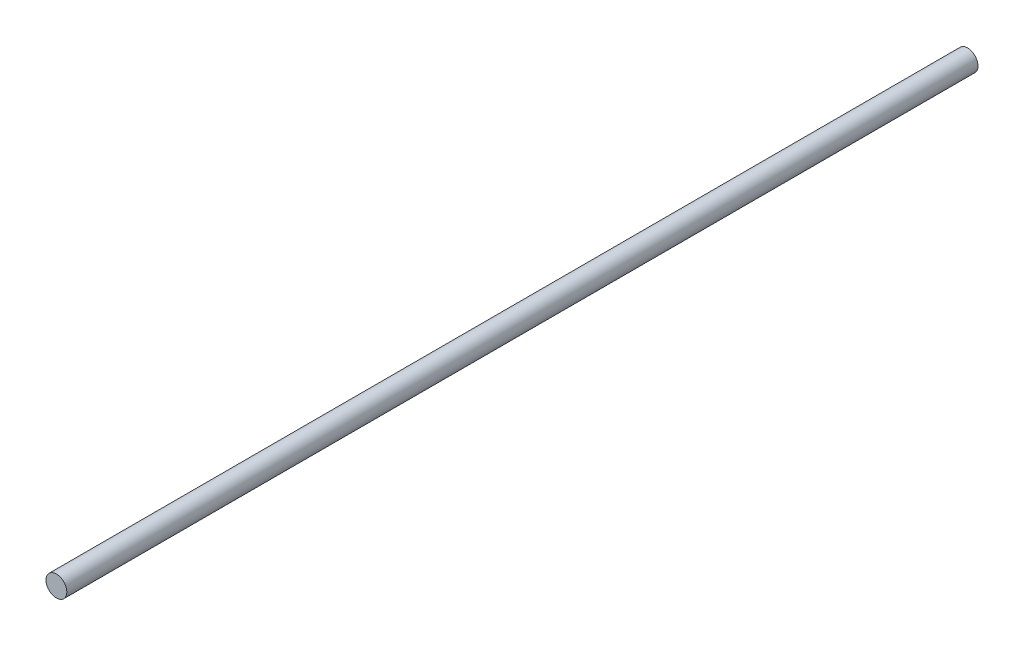
SolidWorks part; units mm, degrees
ref_plane "Alzado" through (0, 0, 0) normal (0, 0, 1) x (1, 0, 0)
ref_plane "Planta" through (0, 0, 0) normal (0, 1, 0) x (1, 0, 0)
ref_plane "Vista lateral" through (0, 0, 0) normal (1, 0, 0) x (0, 0, -1)
sketch "Croquis1" plane through (0, 0, 0) normal (0, 0, 1) x (1, 0, 0)
  circle A0 centre (29.9328, -2.1056) radius 4
  dimension "D1" = 8
extrude "Saliente-Extruir1" add sketch "Croquis1" along normal blind 150 and the other way blind 200
